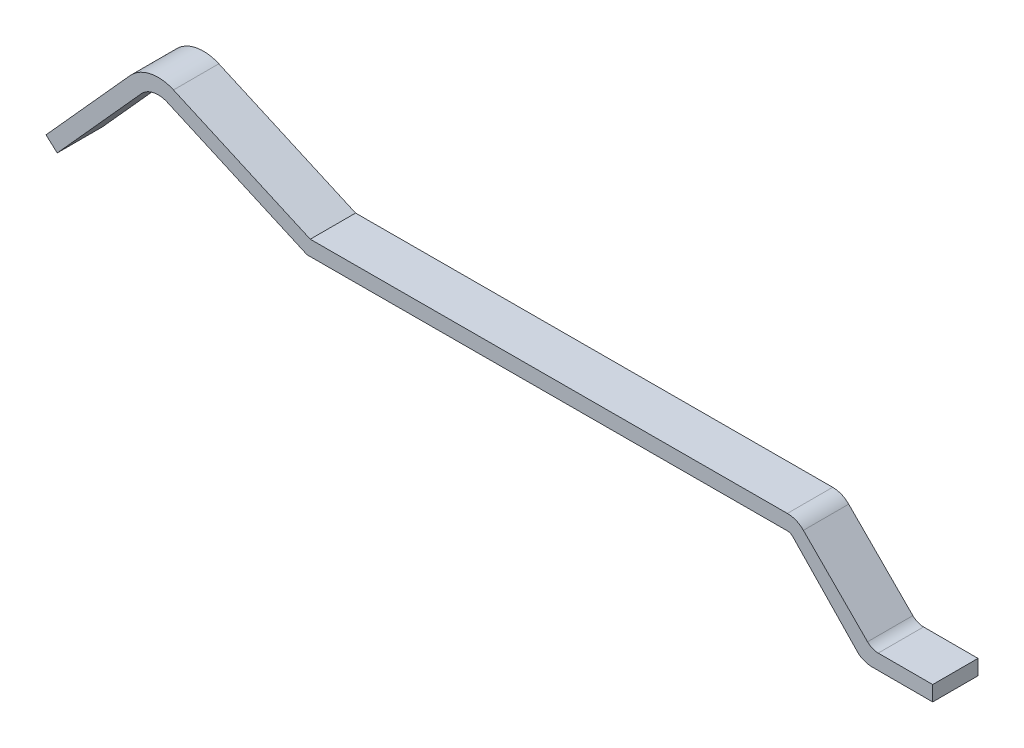
SolidWorks part; units mm, degrees
ref_plane "Plano frontal" through (0, 0, 0) normal (0, 0, 1) x (1, 0, 0)
ref_plane "Plano superior" through (0, 0, 0) normal (0, 1, 0) x (1, 0, 0)
ref_plane "Plano direito" through (0, 0, 0) normal (1, 0, 0) x (0, 0, -1)
sketch "Esboço1" plane through (0, 0, 0) normal (0, 0, 1) x (1, 0, 0)
  line L0 (20.6918, 0.2043) -> (20.6918, 0.0043)
  line L1 (20.6918, 0.0043) -> (19.8918, 0.0043)
  line L3 (19.7118, 0.0643) -> (18.8382, 0.9751)
  line L5 (18.7675, 1.0044) -> (12.4075, 0.99)
  line L8 (12.4075, 0.99) -> (10.558, 1.8135)
  line L11 (10.213, 1.7401) -> (9.0995, 0.5035)
  line L12 (9.0995, 0.5035) -> (8.9509, 0.6373)
  line L13 (8.9509, 0.6373) -> (10.0644, 1.874)
  line L17 (10.6393, 1.9962) -> (12.45, 1.19)
  line L19 (12.45, 1.19) -> (18.7675, 1.2043)
  line L21 (18.9796, 1.1164) -> (19.829, 0.2632)
  line L22 (19.9707, 0.2043) -> (20.6918, 0.2043)
  arc A2 (19.829, 0.2632) -> (19.9707, 0.2043) centre (19.9707, 0.4043) ccw
  arc A3 (19.8918, 0.0043) -> (19.7118, 0.0643) centre (19.8918, 0.3043) cw
  arc A4 (18.7675, 1.0044) -> (18.8382, 0.9751) centre (18.7677, 0.9049) cw
  arc A5 (18.9796, 1.1164) -> (18.7675, 1.2043) centre (18.7682, 0.9059) ccw
  arc A6 (10.558, 1.8135) -> (10.213, 1.7401) centre (10.436, 1.5394) ccw
  arc A7 (10.6393, 1.9962) -> (10.0644, 1.874) centre (10.436, 1.5394) ccw
  dimension "D1" = 0.2
  dimension "D11" = 0.0995
  dimension "D12" = 0.2984
  dimension "D13" = 0.3
  dimension "D2" = 0.8736
  dimension "D3" = 0.8
  dimension "D4" = 0.8494
  dimension "D5" = 0.721
  dimension "D6" = 6.36
  dimension "D7" = 0.0707
  dimension "D8" = 0.18
  dimension "D9" = 0.2121
  dimension "D10" = 0.1417
  dimension "D14" = 0.1999
extrude "Ressalto-extrusão1" add sketch "Esboço1" along normal mid plane 0.6
